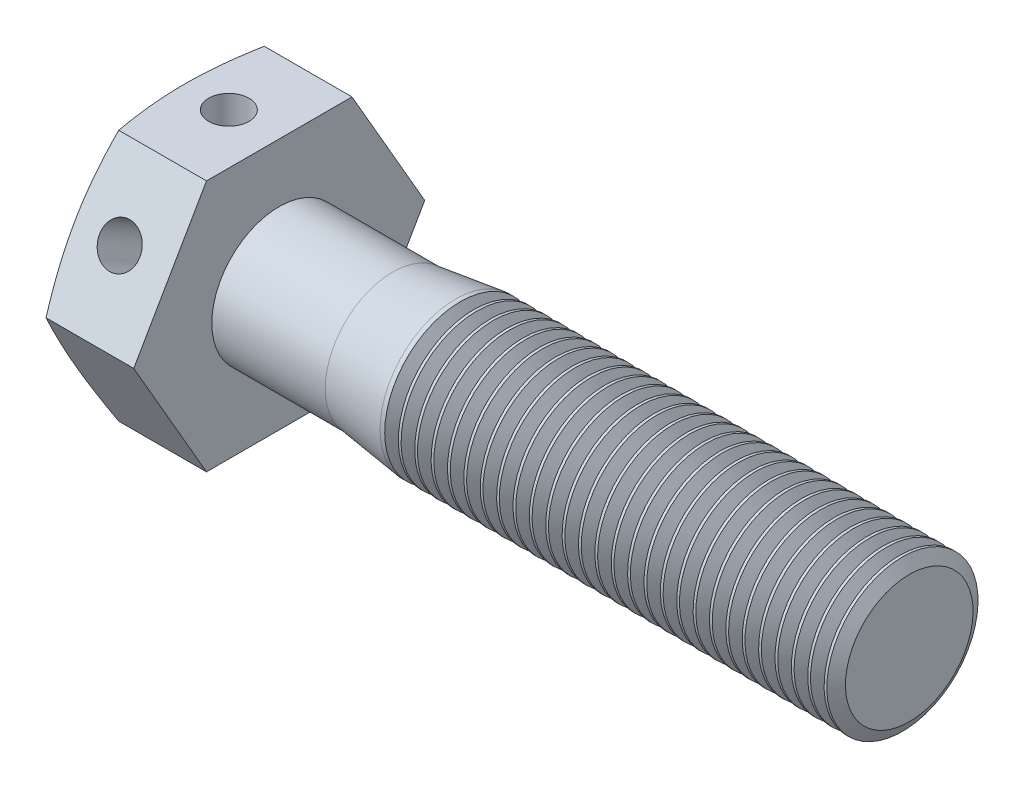
SolidWorks part; units mm, degrees
ref_plane "Front" through (0, 0, 0) normal (0, 0, 1) x (1, 0, 0)
ref_plane "Top" through (0, 0, 0) normal (0, 1, 0) x (1, 0, 0)
ref_plane "Right" through (0, 0, 0) normal (1, 0, 0) x (0, 0, -1)
sketch "Sketch1" plane through (0, 0, 0) normal (1, 0, 0) x (0, 0, -1)
  line L1 (5.7735, 0) -> (2.8868, 5)
  line L2 (2.8868, 5) -> (-2.8868, 5)
  line L3 (-2.8868, 5) -> (-5.7735, 0)
  line L4 (-5.7735, 0) -> (-2.8868, -5)
  line L5 (-2.8868, -5) -> (2.8868, -5)
  line L6 (2.8868, -5) -> (5.7735, 0)
  circle A0 centre (0, 0) radius 5 construction
  dimension "s" = 10
extrude "BaseHead" add sketch "Sketch1" along normal blind 4
ref_plane "Plane1" through (11, 0, 0) normal (1, 0, 0) x (0, 0, -1)
sketch "Sketch2" plane through (4, 0, 0) normal (1, 0, 0) x (0, 0, -1)
  circle A0 centre (0, 0) radius 3
  dimension "d" = 6
extrude "BaseBody" add sketch "Sketch2" along normal blind 25
cosmetic thread "ThreadCosmetic1" [suppressed] parameters "b"=18, "D2"=4.917
sketch "Sketch3" plane through (3.1612, 0, 2.6123) normal (0, 1, 0) x (0, 0, -1)
  line L0 (2.6123, 5.2326) -> (2.6123, 1.6388) construction
  line L2 (8.3858, 3.1612) -> (8.3858, 2.6431)
  line L3 (8.3858, 2.6431) -> (6.9623, 3.1612)
  line L5 (6.9623, 3.1612) -> (8.3858, 3.1612)
  dimension "D1" = 20
  dimension "dw" = 8.7
revolve "HeadChamfer" cut sketch "Sketch3" angle 360 about L0
sketch "Sketch4" plane through (0, 0, 0) normal (-1, 0, 0) x (0, 0, 1)
  circle A0 centre (0, 0) radius 3.4
  dimension "da" = 6.8
extrude "Cut-Extrude1" cut sketch "Sketch4" against normal blind 0.8
sketch "Sketch5" plane through (-2.9296, 0, 7.9296) normal (0, 1, 0) x (0, 0, -1)
  line L0 (7.9296, -0.2325) -> (7.9296, -16.4861) construction
  line L1 (7.9296, -31.9296) -> (7.9296, -6.9296) construction
  line L2 (10.9296, -13.9296) -> (10.6046, -11.4296)
  line L3 (4.9296, -31.9296) -> (10.9296, -31.9296) construction
  line L4 (10.6046, -11.4296) -> (10.6046, -6.9296)
  line L5 (10.9296, -31.9296) -> (10.9296, -6.9296) construction
  line L6 (10.6046, -6.9296) -> (13.2796, -6.9296)
  line L7 (13.2796, -6.9296) -> (13.2796, -13.9296)
  line L8 (13.2796, -13.9296) -> (10.9296, -13.9296)
  line L9 (13.7031, -6.9296) -> (10.8164, -6.9296) construction
  dimension "ds" = 5.35
  dimension "x" = 2.5
  dimension "D4" = 10.7
  dimension "D3" = 18
revolve "Cut-Revolve1" cut sketch "Sketch5" angle 360 about L0
fillet "HeadFillet" [suppressed] radius 0.25
sketch "Sketch6" plane through (0, 0, 0) normal (0, 1, 0) x (1, 0, 0)
  line L0 (-2.6972, 0) -> (13.5564, 0) construction
  line L1 (4, 5.7735) -> (4, 2.8868) construction
  circle A0 centre (2, 0) radius 0.8
  dimension "d1" = 1.6
  dimension "h" = 2
extrude "Hole" cut sketch "Sketch6" against normal through all and the other way through all
pattern_circular "CirPattern1" count 2 over 60 about axis through (-2.6972, 0, 0) along (1, 0, 0) of "Hole"
sketch "Sketch7" plane through (0, 0, 0) normal (0, 0, 1) x (1, 0, 0)
  line L0 (28.7293, 3.2) -> (29.2707, 3.2)
  line L1 (29.2707, 3.2) -> (29.2708, 3)
  line L2 (29.2708, 3) -> (29, 2.531)
  line L3 (28.7293, 3) -> (29, 2.531)
  line L4 (28.7293, 3.2) -> (28.7293, 3)
  line L5 (28.8635, 0) -> (0, 0) construction
  line L6 (28.7293, 3) -> (29.2708, 3) construction
  line L7 (29, 3) -> (29, 2.531) construction
  line L8 (29, -3) -> (29, 3) construction
  line L9 (29, 3) -> (11, 3) construction
  point P5 (29, 3.2)
  dimension "D1" = 0.2
  dimension "D2" = 0.5415
revolve "Cut-Revolve10" cut sketch "Sketch7" angle 360 about L5
pattern_linear "LPattern10" count 28 spacing 0.6498 along (-1, 0, 0) of "Cut-Revolve10"
equation "\"D1@Cut-Extrude1\" = 0.2 * \"k@BaseHead\""
equation "\"b@ThreadCosmetic1\" = \"l@BaseBody\" - \"lg@Plane1\""
equation "\"D4@Sketch5\" = 2 * \"ds@Sketch5\""
equation "\"D3@Sketch5\" =\"l@BaseBody\" - \"lg@Plane1\""
equation "\"D2@Sketch7\" =  ( \"d@Sketch2\" - \"D2@ThreadCosmetic1\" )  / 2"
equation "\"D3@LPattern10\" = \"D2@Sketch7\" * 1.2"
equation "\"D1@LPattern10\" = \"b@ThreadCosmetic1\" / \"D3@LPattern10\""
